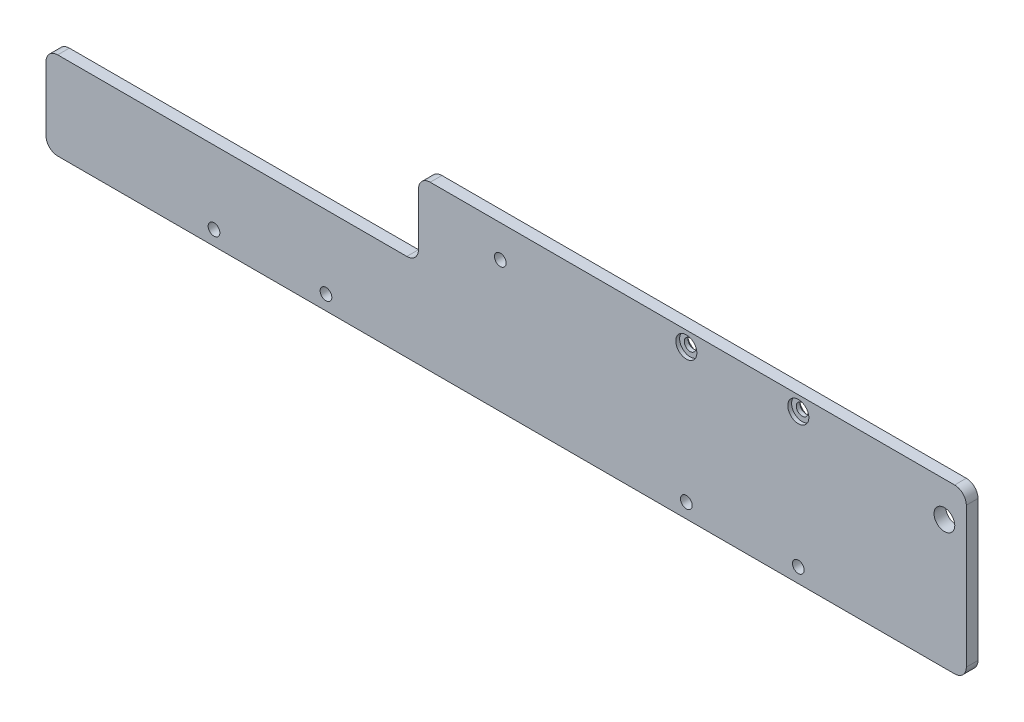
SolidWorks part; units mm, degrees
ref_plane "前视基准面" through (0, 0, 0) normal (0, 0, 1) x (1, 0, 0)
ref_plane "上视基准面" through (0, 0, 0) normal (0, 1, 0) x (1, 0, 0)
ref_plane "右视基准面" through (0, 0, 0) normal (1, 0, 0) x (0, 0, -1)
sketch "草图1" plane through (0, 0, 0) normal (0, 0, 1) x (1, 0, 0)
  line L0 (-27.1941, 11.0961) -> (-27.1941, -12.4101) construction
  line L1 (126.3059, -12.4101) -> (-180.6941, -12.4101)
  line L2 (130.3059, -8.4101) -> (130.3059, 7.7119)
  line L3 (-37.1941, 17.5899) -> (-180.6941, 17.5899)
  line L4 (-184.6941, -8.4101) -> (-184.6941, 13.5899)
  line L5 (130.3059, -12.4101) -> (-184.6941, 17.5899) construction
  line L6 (72.7628, 4.8891) -> (-184.6941, -12.4101) construction
  line L7 (130.3059, 17.5899) -> (130.3059, 7.7119)
  line L10 (-23.1941, 43.5899) -> (126.3059, 43.5899)
  line L11 (130.3059, 17.5899) -> (130.3059, 39.5899)
  line L13 (-27.1941, 39.5899) -> (-27.1941, 27.5899)
  circle A0 centre (-127.1941, -7.4101) radius 2
  circle A1 centre (-88.8641, -7.4101) radius 2
  circle A2 centre (34.4759, -7.4101) radius 2
  circle A3 centre (72.8059, -7.4101) radius 2
  arc A4 (126.3059, -12.4101) -> (130.3059, -8.4101) centre (126.3059, -8.4101) ccw
  arc A6 (-180.6941, -12.4101) -> (-184.6941, -8.4101) centre (-180.6941, -8.4101) cw
  arc A7 (-184.6941, 13.5899) -> (-180.6941, 17.5899) centre (-180.6941, 13.5899) cw
  arc A8 (130.3059, 39.5899) -> (126.3059, 43.5899) centre (126.3059, 39.5899) ccw
  arc A9 (-23.1941, 43.5899) -> (-27.1941, 39.5899) centre (-23.1941, 39.5899) ccw
  circle A11 centre (34.4759, 38.5899) radius 2
  circle A12 centre (72.8059, 38.5899) radius 2
  circle A13 centre (122.8059, 31.5899) radius 3.55
  arc A14 (-37.1941, 17.5899) -> (-27.1941, 27.5899) centre (-37.1941, 27.5899) ccw
  point P0 (0, 0)
  point P33 (130.3059, 43.5899)
  point P36 (-27.1941, 43.5899)
  dimension "D3" = 4
  dimension "D4" = 4
  dimension "D5" = 38.33
  dimension "D6" = 5
  dimension "D7" = 200
  dimension "D8" = 4
  dimension "D9" = 4
  dimension "D10" = 4
  dimension "D11" = 4
  dimension "D12" = 46
  dimension "D13" = 46
  dimension "D15" = 7.1
  dimension "D16" = 7.5
  dimension "D17" = 44
  dimension "D18" = 10
  dimension "D1" = 157.5
  dimension "300" = 315
  dimension "D2" = 30
  dimension "D14" = 56
extrude "凸台-拉伸1" add sketch "草图1" along normal blind 4
sketch "草图2" plane through (0, 0, 0) normal (0, 0, -1) x (-1, 0, 0)
  line L0 (37.1941, 17.5899) -> (180.6941, 17.5899) construction
  line L1 (23.1941, 43.5899) -> (53.1941, 43.5899)
  line L2 (23.1941, 43.5899) -> (23.1941, 17.5899)
  line L3 (23.1941, 17.5899) -> (57.1941, 17.5899)
  line L4 (57.1941, 39.5899) -> (57.1941, 21.5899)
  line L5 (61.1941, 17.5899) -> (83.3103, 17.5899)
  line L6 (57.1941, 17.5899) -> (61.1941, 17.5899)
  arc A0 (61.1941, 17.5899) -> (57.1941, 21.5899) centre (61.1941, 21.5899) cw
  arc A1 (57.1941, 39.5899) -> (53.1941, 43.5899) centre (53.1941, 39.5899) ccw
  dimension "D1" = 4
  dimension "D2" = 30
extrude "凸台-拉伸3" add sketch "草图2" against normal blind 4
sketch "草图3" plane through (0, 0, 0) normal (0, 0, -1) x (-1, 0, 0)
  circle A0 centre (-72.8059, 38.5899) radius 3.6
  circle A1 centre (-34.4759, 38.5899) radius 3.6
  dimension "D1" = 7.2
  dimension "D2" = 7.2
extrude "切除-拉伸1" cut sketch "草图3" against normal blind 1.4
sketch "草图7" plane through (0, 0, 0) normal (0, 0, -1) x (-1, 0, 0)
  line L0 (-126.3059, -12.4101) -> (180.6941, -12.4101) construction
  line L1 (57.1941, 39.5899) -> (57.1941, 21.5899) construction
  circle A0 centre (29.1941, 32.5899) radius 2
  dimension "D1" = 4
  dimension "D2" = 45
  dimension "D3" = 28
extrude "切除-拉伸2" cut sketch "草图7" against normal blind 10
sketch "草图8" plane through (0, 0, 4) normal (0, 0, 1) x (1, 0, 0)
  circle A0 centre (72.8059, 38.5899) radius 3.6
  circle A1 centre (34.4759, 38.5899) radius 3.6
extrude "切除-拉伸3" cut sketch "草图8" against normal blind 1.3
